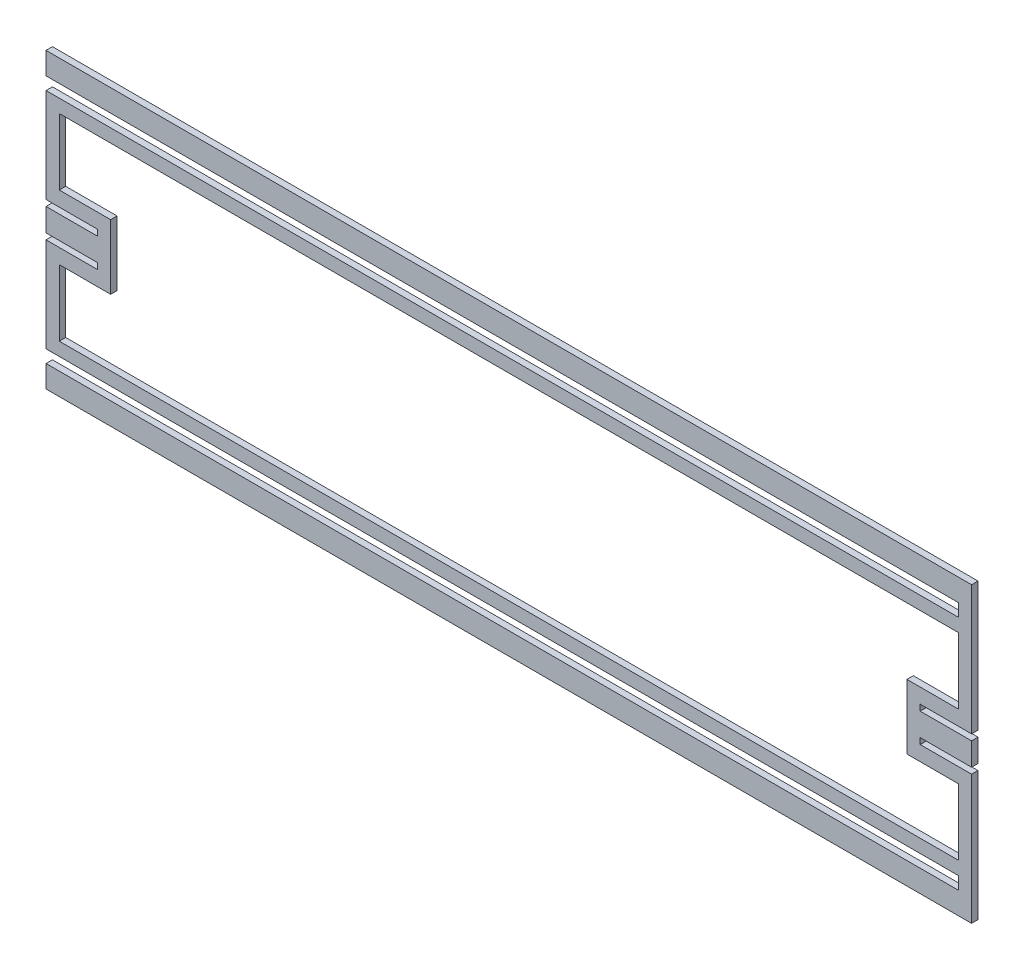
SolidWorks part; units mm, degrees
ref_plane "Front" through (0, 0, 0) normal (0, 0, 1) x (1, 0, 0)
ref_plane "Top" through (0, 0, 0) normal (0, 1, 0) x (1, 0, 0)
ref_plane "Right" through (0, 0, 0) normal (1, 0, 0) x (0, 0, -1)
sketch "Sketch1" plane through (0, 0, 0) normal (0, 0, 1) x (1, 0, 0)
  line L0 (-228.7016, 8.6296) -> (-203.3016, 8.6296)
  line L1 (-203.3016, 8.6296) -> (-203.3016, 5.6579)
  line L2 (-203.3016, 5.6579) -> (-228.7016, 5.6578)
  line L3 (-228.7016, 5.6578) -> (-228.7016, -5.6578)
  line L4 (-228.7016, -5.6578) -> (-203.3016, -5.6579)
  line L5 (-203.3016, -5.6579) -> (-203.3016, -8.6297)
  line L6 (-203.3016, -8.6297) -> (-228.7016, -8.6297)
  line L7 (-228.7016, -8.6297) -> (-228.7016, -55.2736)
  line L8 (-228.7016, -55.2736) -> (222.1484, -55.2736)
  line L9 (222.1484, -55.2736) -> (222.1484, -61.5474)
  line L10 (222.1484, -61.5474) -> (-228.7016, -61.5474)
  line L11 (-228.7016, -61.5474) -> (-228.7016, -72.4662)
  line L12 (-228.7016, -72.4662) -> (228.7016, -72.4662)
  line L13 (228.7016, -72.4662) -> (228.7016, -8.6297)
  line L14 (228.7016, -8.6297) -> (203.3016, -8.6297)
  line L15 (203.3016, -8.6297) -> (203.3016, -5.6579)
  line L16 (203.3016, -5.6579) -> (228.7016, -5.6578)
  line L17 (228.7016, -5.6578) -> (228.7016, 5.6578)
  line L18 (228.7016, 5.6578) -> (203.3016, 5.6579)
  line L19 (203.3016, 5.6579) -> (203.3016, 8.6296)
  line L20 (203.3016, 8.6296) -> (228.7016, 8.6296)
  line L21 (228.7016, 8.6296) -> (228.7016, 72.4662)
  line L22 (228.7016, 72.4662) -> (-228.7016, 72.4662)
  line L23 (-228.7016, 72.4662) -> (-228.7016, 61.5474)
  line L24 (-228.7016, 61.5474) -> (222.1484, 61.5474)
  line L25 (222.1484, 61.5474) -> (222.1484, 55.2736)
  line L26 (222.1484, 55.2736) -> (-228.7016, 55.2736)
  line L27 (-228.7016, 55.2736) -> (-228.7016, 8.6296)
  line L28 (222.1484, -48.7204) -> (222.1484, -15.9766)
  line L29 (222.1484, -15.9766) -> (196.7484, -15.9766)
  line L30 (196.7484, -15.9766) -> (196.7484, 15.9766)
  line L31 (196.7484, 15.9766) -> (222.1484, 15.9766)
  line L32 (222.1484, 15.9766) -> (222.1484, 48.7204)
  line L33 (-222.1484, -48.7204) -> (222.1484, -48.7204)
  line L34 (-222.1484, -15.9766) -> (-222.1484, -48.7204)
  line L35 (-196.7484, -15.9766) -> (-222.1484, -15.9766)
  line L36 (-196.7484, 15.9766) -> (-196.7484, -15.9766)
  line L37 (-222.1484, 15.9766) -> (-196.7484, 15.9766)
  line L38 (-222.1484, 48.7204) -> (-222.1484, 15.9766)
  line L39 (222.1484, 48.7204) -> (-222.1484, 48.7204)
extrude "Boss-Extrude1" add sketch "Sketch1" along normal blind 3.175
